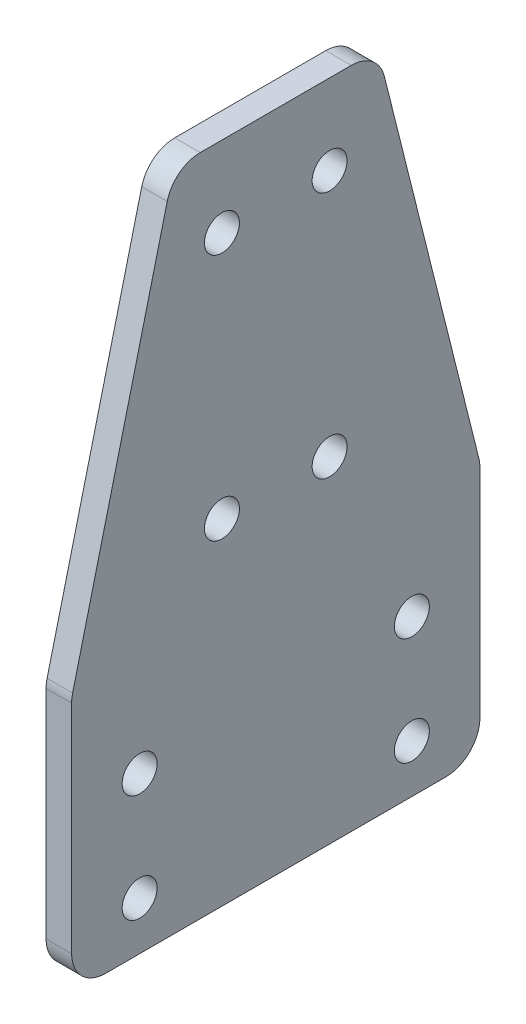
SolidWorks part; units mm, degrees
material "Alloy Steel"
ref_plane "Front Plane" through (0, 0, 0) normal (0, 0, 1) x (1, 0, 0)
ref_plane "Top Plane" through (0, 0, 0) normal (0, 1, 0) x (1, 0, 0)
ref_plane "Right Plane" through (0, 0, 0) normal (1, 0, 0) x (0, 0, -1)
ref_plane "Front Plane-Master Sketch" through (0, 0, 0) normal (0, 0, 1) x (1, 0, 0)
ref_plane "Top Plane-Master Sketch" through (0, 0, 0) normal (0, 1, 0) x (1, 0, 0)
ref_plane "Right Plane-Master Sketch" through (0, 0, 0) normal (1, 0, 0) x (0, 0, -1)
sketch "Y axis top-Master Sketch" plane through (0, 0, 0) normal (0, 1, 0) x (1, 0, 0)
  line L0 (140.4, -200) -> (120.4, -200)
  line L1 (-230.1875, -245) -> (230.1875, -245)
  line L2 (-230.1875, -245) -> (-230.1875, 245)
  line L3 (-230.1875, 245) -> (230.1875, 245)
  line L4 (230.1875, -245) -> (230.1875, 245)
  line L5 (0, 245) -> (0, -245) construction
  line L6 (-230.1875, 0) -> (230.1875, 0) construction
  line L7 (-8, 236.05) -> (8, 236.05)
  line L8 (-8, 236.05) -> (-8, -163.95)
  line L9 (-8, -163.95) -> (8, -163.95)
  line L10 (8, 236.05) -> (8, -163.95)
  line L11 (-140.4, 200) -> (-120.4, 200)
  line L12 (-140.4, 200) -> (-140.4, -200)
  line L13 (-140.4, -200) -> (-120.4, -200)
  line L14 (-120.4, 200) -> (-120.4, -200)
  line L15 (120.4, 200) -> (120.4, -200)
  line L16 (140.4, 200) -> (120.4, 200)
  line L17 (140.4, 200) -> (140.4, -200)
  line L18 (-230.1875, 206.9) -> (230.1875, 206.9)
  line L19 (-230.1875, -206.9) -> (230.1875, -206.9)
  line L20 (-192.0875, 206.9) -> (-192.0875, -206.9)
  line L21 (192.0875, 206.9) -> (192.0875, -206.9)
  line L22 (230.1875, 149.75) -> (192.0875, 149.75)
  line L27 (-152.4, -152.4) -> (152.4, -152.4)
  line L28 (-152.4, -152.4) -> (-152.4, 152.4)
  line L29 (-152.4, 152.4) -> (152.4, 152.4)
  line L34 (152.4, -152.4) -> (152.4, 152.4)
  line L35 (0, 152.4) -> (0, -152.4) construction
  line L36 (-152.4, 0) -> (152.4, 0) construction
  line L37 (-230.1875, 187.85) -> (-192.0875, 187.85)
  line L38 (-230.1875, 187.85) -> (-230.1875, 149.75)
  line L39 (-28.2, 324.7625) -> (28.2, 324.7625)
  line L40 (-28.2, 324.7625) -> (-28.2, 249.7625)
  line L41 (-28.2, 249.7625) -> (28.2, 249.7625)
  line L42 (28.2, 324.7625) -> (28.2, 249.7625)
  line L43 (-26, -20) -> (26, -20)
  line L44 (-26, -20) -> (-26, 20)
  line L45 (-26, 20) -> (26, 20)
  line L46 (26, -20) -> (26, 20)
  line L47 (0, 20) -> (0, -20) construction
  line L48 (-26, 0) -> (26, 0) construction
  line L49 (-230.1875, 149.75) -> (-192.0875, 149.75)
  line L50 (-192.0875, 187.85) -> (-192.0875, 149.75)
  line L51 (192.0875, 187.85) -> (192.0875, 149.75)
  line L52 (230.1875, 187.85) -> (192.0875, 187.85)
  line L53 (230.1875, 187.85) -> (230.1875, 149.75)
  line L55 (-230.1875, 206.9) -> (-234.95, 206.9)
  line L56 (-234.95, 206.9) -> (-234.95, 130.7)
  line L57 (-234.95, 130.7) -> (-230.1875, 130.7)
  point P0 (0, 0)
  point P8 (0, 236.05)
  point P32 (0, 0)
  point P33 (0, 324.7625)
  point P34 (0, 0)
  point P52 (-230.1875, 168.8)
  point P53 (-234.95, 168.8)
  point P56 (-120.4, 0)
  dimension "D3" = 16
  dimension "D4" = 400
  dimension "D5" = 20
  dimension "D6" = 400
  dimension "D7" = 38.1
  dimension "D8" = 38.1
  dimension "D9" = 38.1
  dimension "D10" = 12
  dimension "D11" = 56.4
  dimension "D12" = 75
  dimension "D13" = 4.7625
  dimension "D14" = 304.8
  dimension "D15" = 52
  dimension "D16" = 40
  dimension "D17" = 45
  dimension "D18" = 304.8
  dimension "D19" = 4.7625
  dimension "D20" = 19.05
  dimension "D22" = 8.95
  dimension "D23" = 460.375
ref_plane "X axis plane-Master Sketch" through (-212.3, 0, -100.693) normal (0, 0, -1) x (-1, 0, 0)
sketch "Y axis side-Master Sketch" plane through (0, 0, 0) normal (0, 0, 1) x (1, 0, 0)
  line L0 (-230.1875, 0) -> (-230.1875, 47.625)
  line L3 (-230.1875, 0) -> (-192.0875, 0)
  line L4 (-23.5, 93.125) -> (-23.5, 46.125) construction
  line L6 (-230.1875, 38.1) -> (230.1875, 38.1)
  line L7 (230.1875, 0) -> (230.1875, 47.625)
  line L8 (-192.0875, 0) -> (-192.0875, 38.1)
  line L12 (230.1875, 0) -> (230.1875, 47.625)
  line L14 (230.1875, 0) -> (192.0875, 0)
  line L33 (192.0875, 0) -> (192.0875, 38.1)
  line L34 (-23.5, 46.125) -> (23.5, 46.125) construction
  line L41 (-230.1875, 47.625) -> (230.1875, 47.625)
  line L42 (-140.4, 47.625) -> (-140.4, 65.125)
  line L47 (-140.4, 65.125) -> (-120.4, 65.125)
  line L48 (-120.4, 65.125) -> (-120.4, 47.625)
  line L49 (140.4, 47.625) -> (140.4, 65.125)
  line L50 (140.4, 65.125) -> (120.4, 65.125)
  line L51 (120.4, 65.125) -> (120.4, 47.625)
  line L52 (-28.2, 41.425) -> (-28.2, 97.825)
  line L53 (-28.2, 97.825) -> (28.2, 97.825)
  line L54 (28.2, 97.825) -> (28.2, 41.425)
  line L55 (-152.4, 77.625) -> (-152.4, 52.225)
  line L56 (-152.4, 52.225) -> (-140.4, 52.225)
  line L57 (-152.4, 77.625) -> (-108.4, 77.625)
  line L58 (-108.4, 77.625) -> (-108.4, 52.225)
  line L59 (-108.4, 52.225) -> (-120.4, 52.225)
  line L60 (152.4, 52.225) -> (140.4, 52.225)
  line L61 (152.4, 77.625) -> (152.4, 52.225)
  line L62 (152.4, 77.625) -> (108.4, 77.625)
  line L63 (108.4, 77.625) -> (108.4, 52.225)
  line L64 (108.4, 52.225) -> (120.4, 52.225)
  line L65 (-28.2, 41.425) -> (28.2, 41.425)
  line L66 (-26, 49.625) -> (26, 49.625)
  line L67 (-26, 49.625) -> (-26, 89.625)
  line L68 (-26, 89.625) -> (26, 89.625)
  line L69 (26, 49.625) -> (26, 89.625)
  line L70 (0, 89.625) -> (0, 49.625) construction
  line L71 (-26, 69.625) -> (26, 69.625) construction
  line L73 (-152.4, 77.625) -> (-108.4, 77.625)
  line L74 (-152.4, 77.625) -> (-152.4, 89.625)
  line L75 (-152.4, 89.625) -> (-108.4, 89.625)
  line L76 (-108.4, 77.625) -> (-108.4, 89.625)
  line L77 (108.4, 77.625) -> (152.4, 77.625)
  line L78 (108.4, 77.625) -> (108.4, 89.625)
  line L79 (108.4, 89.625) -> (152.4, 89.625)
  line L80 (152.4, 77.625) -> (152.4, 89.625)
  line L85 (-152.4, 89.625) -> (152.4, 89.625)
  line L86 (-152.4, 89.625) -> (-152.4, 102.325)
  line L87 (-152.4, 102.325) -> (152.4, 102.325)
  line L88 (152.4, 89.625) -> (152.4, 102.325)
  circle A12 centre (0, 69.625) radius 6
  circle A13 centre (-23.5, 93.125) radius 2.5
  circle A14 centre (23.5, 93.125) radius 2.5
  circle A15 centre (23.5, 46.125) radius 2.5
  circle A16 centre (-23.5, 46.125) radius 2.5
  point P16 (0, 46.125)
  point P19 (-23.5, 69.625)
  point P90 (0, 97.825)
  point P91 (-28.2, 69.625)
  point P121 (0, 89.625)
  dimension "D20" = 12
  dimension "D24" = 22
  dimension "D5" = 5
  dimension "D3" = 38.1
  dimension "D4" = 47
  dimension "D16" = 9.525
  dimension "D18" = 17.5
  dimension "D19" = 56.4
  dimension "D21" = 44
  dimension "D22" = 30
  dimension "D23" = 4.6
  dimension "D25" = 40
  dimension "D26" = 52
  dimension "D28" = 12.7
sketch "X axis front-Master Sketch" plane through (-396.45, 0, -100.693) normal (0, 0, -1) x (-1, 0, 0)
  line L0 (-184.15, 47.625) -> (-184.15, 390.525)
  line L1 (-184.15, 390.525) -> (-222.25, 390.525)
  line L2 (-222.25, 390.525) -> (-222.25, 47.625)
  line L4 (-414.3375, 0) -> (-414.3375, 246.425) construction
  line L5 (-644.525, 47.625) -> (-644.525, 390.525)
  line L6 (-644.525, 390.525) -> (-606.425, 390.525)
  line L7 (-606.425, 390.525) -> (-606.425, 47.625)
  line L8 (-222.25, 390.525) -> (-606.425, 390.525)
  line L9 (-222.25, 352.425) -> (-606.425, 352.425)
  line L10 (-222.25, 284.525) -> (-606.425, 284.525)
  line L11 (-222.25, 246.425) -> (-606.425, 246.425)
  line L12 (-414.3375, 390.525) -> (-414.3375, 352.425) construction
  line L13 (-414.3375, 284.525) -> (-414.3375, 246.425) construction
  line L14 (-414.3375, 352.425) -> (-414.3375, 284.525) construction
  line L15 (-614.3375, 381.475) -> (-214.3375, 381.475)
  line L16 (-614.3375, 381.475) -> (-614.3375, 361.475)
  line L17 (-614.3375, 361.475) -> (-214.3375, 361.475)
  line L18 (-214.3375, 381.475) -> (-214.3375, 361.475)
  line L19 (-614.3375, 275.475) -> (-214.3375, 275.475)
  line L20 (-614.3375, 275.475) -> (-614.3375, 255.475)
  line L21 (-614.3375, 255.475) -> (-214.3375, 255.475)
  line L22 (-214.3375, 275.475) -> (-214.3375, 255.475)
  line L23 (-614.3375, 326.475) -> (-214.3375, 326.475)
  line L24 (-614.3375, 326.475) -> (-614.3375, 310.475)
  line L25 (-614.3375, 310.475) -> (-214.3375, 310.475)
  line L26 (-214.3375, 326.475) -> (-214.3375, 310.475)
  line L27 (-184.15, 47.625) -> (-222.25, 47.625)
  line L28 (-606.425, 47.625) -> (-644.525, 47.625)
  line L29 (-434.3375, 344.475) -> (-394.3375, 344.475)
  line L30 (-434.3375, 344.475) -> (-434.3375, 292.475)
  line L31 (-434.3375, 292.475) -> (-394.3375, 292.475)
  line L32 (-394.3375, 344.475) -> (-394.3375, 292.475)
  point P24 (-414.3375, 344.475)
  point P25 (-614.3375, 265.475)
  point P30 (-614.3375, 371.475)
  point P31 (-414.3375, 371.475)
  point P36 (-414.3375, 265.475)
  point P41 (-414.3375, 326.475)
  point P42 (-414.3375, 318.475)
  point P43 (-614.3375, 318.475)
  point P44 (-394.3375, 318.475)
  point P45 (-214.3375, 318.475)
  point P51 (-414.3375, 381.475)
  dimension "D1" = 38.1
  dimension "D2" = 400
  dimension "D3" = 20
  dimension "D4" = 16
  dimension "D5" = 40
  dimension "D6" = 52
  dimension "D7" = 35
  dimension "D8" = 342.9
sketch "X axis side-Master Sketch" plane through (0, 0, 0) normal (1, 0, 0) x (0, 0, -1)
  line L1 (144.9875, 381.475) -> (127.4875, 381.475)
  line L2 (144.9875, 381.475) -> (144.9875, 361.475)
  line L3 (144.9875, 361.475) -> (127.4875, 361.475)
  line L4 (127.4875, 381.475) -> (127.4875, 361.475)
  line L5 (140.3875, 381.475) -> (140.3875, 393.475)
  line L6 (140.3875, 393.475) -> (114.9875, 393.475)
  line L7 (114.9875, 393.475) -> (114.9875, 349.475)
  line L8 (144.9875, 371.475) -> (127.4875, 371.475) construction
  line L10 (140.3875, 349.475) -> (114.9875, 349.475)
  line L11 (140.3875, 361.475) -> (140.3875, 349.475)
  line L12 (149.75, 390.525) -> (144.9875, 390.525)
  line L14 (144.9875, 390.525) -> (144.9875, 352.425)
  line L15 (144.9875, 352.425) -> (149.75, 352.425)
  line L17 (149.75, 318.475) -> (122.9875, 318.475) construction
  line L18 (144.9875, 284.525) -> (149.75, 284.525)
  line L19 (144.9875, 246.425) -> (144.9875, 284.525)
  line L20 (149.75, 246.425) -> (144.9875, 246.425)
  line L21 (140.3875, 275.475) -> (140.3875, 287.475)
  line L22 (140.3875, 287.475) -> (114.9875, 287.475)
  line L23 (114.9875, 243.475) -> (114.9875, 287.475)
  line L24 (140.3875, 243.475) -> (114.9875, 243.475)
  line L25 (140.3875, 255.475) -> (140.3875, 243.475)
  line L26 (127.4875, 255.475) -> (127.4875, 275.475)
  line L27 (144.9875, 275.475) -> (127.4875, 275.475)
  line L28 (144.9875, 255.475) -> (144.9875, 275.475)
  line L29 (144.9875, 255.475) -> (127.4875, 255.475)
  line L31 (102.9875, 344.475) -> (142.9875, 344.475)
  line L32 (102.9875, 344.475) -> (102.9875, 292.475)
  line L33 (102.9875, 292.475) -> (142.9875, 292.475)
  line L34 (142.9875, 344.475) -> (142.9875, 292.475)
  line L35 (102.9875, 493.475) -> (96.6375, 493.475)
  line L36 (102.9875, 493.475) -> (102.9875, 243.475)
  line L37 (102.9875, 243.475) -> (96.6375, 243.475)
  line L38 (96.6375, 493.475) -> (96.6375, 243.475)
  circle A0 centre (122.9875, 318.475) radius 6
  point P14 (114.9875, 265.475)
  point P16 (114.9875, 371.475)
  point P48 (122.9875, 292.475)
  dimension "D7" = 12
  dimension "D9" = 22
  dimension "D1" = 4.7625
  dimension "D2" = 17.5
  dimension "D3" = 12
  dimension "D4" = 12.5
  dimension "D5" = 25.4
  dimension "D6" = 40
  dimension "D8" = 6.35
  dimension "D10" = 250
ref_plane "Z axis front plane-Master Sketch" through (0, 556.975, -47.5805) normal (0, 0, 1) x (1, 0, 0)
sketch "Z axis front-Master Sketch" plane through (0, 556.975, -47.5805) normal (0, 0, 1) x (1, 0, 0)
  line L0 (0, 48.55) -> (0, -276.85) construction
  line L1 (-103, 48.55) -> (103, 48.55)
  line L2 (-103, 48.55) -> (-103, -276.85)
  line L3 (-103, -276.85) -> (103, -276.85)
  line L4 (103, 48.55) -> (103, -276.85)
  line L5 (-88, 35.85) -> (-68, 35.85)
  line L6 (-88, 35.85) -> (-88, -264.15)
  line L7 (-88, -264.15) -> (-68, -264.15)
  line L8 (-68, 35.85) -> (-68, -264.15)
  line L9 (88, -264.15) -> (68, -264.15)
  line L10 (68, 35.85) -> (68, -264.15)
  line L11 (88, 35.85) -> (68, 35.85)
  line L12 (88, 35.85) -> (88, -264.15)
  line L13 (-103, -114.15) -> (103, -114.15) construction
  line L14 (-8, -20.3536) -> (8, -20.3536)
  line L15 (-8, -20.3536) -> (-8, -229.2947)
  line L16 (-8, -229.2947) -> (8, -229.2947)
  line L17 (8, -20.3536) -> (8, -229.2947)
  line L19 (-26, -43.6221) -> (26, -43.6221)
  line L20 (-26, -43.6221) -> (-26, -83.6221)
  line L21 (-26, -83.6221) -> (26, -83.6221)
  line L22 (26, -43.6221) -> (26, -83.6221)
  point P20 (0, -20.3536)
  point P27 (0, -43.6221)
  dimension "D1" = 15
  dimension "D2" = 20
  dimension "D3" = 300
  dimension "D4" = 16
  dimension "D5" = 40
  dimension "D6" = 52
  dimension "D7" = 42
  dimension "D8" = 12.7
  dimension "D10" = 12.7
ref_plane "Z axis side plane-Master Sketch" through (-101, 417.8187, -47.5805) normal (0, -1, 0) x (-1, 0, 0)
inserted part "Master Sketch"
move or copy body "Body-Move/Copy2"
ref_plane "Plane1" through (-230.1875, 0, 0) normal (1, 0, 0) x (0, 0, -1)
sketch "Sketch1" plane through (-230.1875, 0, 0) normal (1, 0, 0) x (0, 0, -1)
  line L0 (130.7, 0) -> (206.9, 0)
  line L1 (-245, 0) -> (245, 0) construction
  line L2 (-245, 0) -> (245, 0) construction
  line L3 (187.85, 0) -> (149.75, 0) construction
  line L4 (206.9, 0) -> (206.9, 47.625)
  line L6 (130.7, 47.625) -> (130.7, 0)
  line L7 (206.9, 47.625) -> (187.85, 123.825)
  line L8 (187.85, 123.825) -> (149.75, 123.825)
  line L9 (149.75, 123.825) -> (130.7, 47.625)
  line L11 (143.4, 38.1) -> (-238.65, 38.1) construction
  line L13 (158.75, 108.825) -> (158.75, 123.825) construction
  line L15 (149.75, 390.525) -> (149.75, 38.1) construction
  line L16 (168.8, 123.825) -> (168.8, 0) construction
  line L17 (178.85, 108.825) -> (158.75, 108.825) construction
  line L18 (238.65, 47.625) -> (194.2, 47.625) construction
  circle A0 centre (194.2, 29.1) radius 3.2639
  circle A2 centre (158.75, 108.825) radius 3.2639
  circle A5 centre (178.85, 108.825) radius 3.2639
  circle A6 centre (178.85, 85.725) radius 3.2639 construction
  circle A7 centre (178.85, 62.625) radius 3.2639
  circle A8 centre (158.75, 85.725) radius 3.2639 construction
  circle A9 centre (158.75, 62.625) radius 3.2639
  circle A10 centre (168.8, 29.1) radius 3.2639 construction
  circle A11 centre (143.4, 29.1) radius 3.2639
  circle A12 centre (168.8, 9) radius 3.2639 construction
  circle A13 centre (143.4, 9) radius 3.2639
  circle A14 centre (194.2, 9) radius 3.2639
  point P8 (168.8, 0)
  point P9 (168.8, 123.825)
  point P44 (168.8, 108.825)
  dimension "D3" = 6.5278
  dimension "D2" = 76.2
  dimension "D7" = 12.7
  dimension "D1" = 15
  dimension "D4" = 9
  dimension "D8" = 15
  dimension "D9" = 9
  dimension "D10" = 9
  dimension "D12" = 2
  dimension "D5" = 3
  dimension "D11" = 3
  dimension "D6" = 2
extrude "Boss-Extrude1" add sketch "Sketch1" against normal up to vertex
sketch "Sketch3" plane through (-234.95, 0, 0) normal (-1, 0, 0) x (0, 0, 1)
  line L0 (-187.85, 123.825) -> (-187.85, 198.825)
  line L1 (-187.85, 198.825) -> (-149.75, 198.825)
  line L2 (-149.75, 198.825) -> (-30.7, 38.1)
  line L3 (-30.7, 38.1) -> (-30.7, 0)
  line L4 (-30.7, 0) -> (-130.7, 0)
  line L5 (-130.7, 47.625) -> (-130.7, 0) construction
  line L6 (-149.75, 123.825) -> (-130.7, 47.625) construction
  line L7 (-187.85, 123.825) -> (-149.75, 123.825) construction
  line L8 (-130.7, 47.625) -> (-130.7, 0)
  line L9 (-149.75, 123.825) -> (-130.7, 47.625)
  line L10 (-187.85, 123.825) -> (-149.75, 123.825)
  line L11 (-178.85, 108.825) -> (-178.85, 62.625) construction
  line L12 (-158.75, 108.825) -> (-158.75, 62.625) construction
  line L13 (-178.85, 198.825) -> (-178.85, 189.825) construction
  line L14 (-178.85, 189.825) -> (-187.85, 189.825) construction
  line L15 (-178.85, 108.825) -> (-178.85, 149.325) construction
  line L16 (-178.85, 149.325) -> (-178.85, 189.825) construction
  line L17 (-194.2, 9) -> (-143.4, 9) construction
  line L18 (-143.4, 29.1) -> (-194.2, 29.1) construction
  line L19 (-143.4, 29.1) -> (-91.55, 29.1) construction
  line L20 (-91.55, 29.1) -> (-39.7, 29.1) construction
  line L21 (-39.7, 9) -> (-30.7, 9) construction
  line L22 (-39.7, 9) -> (-39.7, 0) construction
  circle A0 centre (-158.75, 108.825) radius 3.2639 construction
  circle A1 centre (-178.85, 62.625) radius 3.2639 construction
  circle A2 centre (-178.85, 149.325) radius 3.2639
  circle A3 centre (-178.85, 189.825) radius 3.2639
  circle A4 centre (-158.75, 189.825) radius 3.2639
  circle A5 centre (-158.75, 149.325) radius 3.2639
  circle A6 centre (-91.55, 29.1) radius 3.2639
  circle A7 centre (-39.7, 29.1) radius 3.2639
  circle A8 centre (-39.7, 9) radius 3.2639
  circle A9 centre (-91.55, 9) radius 3.2639
  circle A10 centre (-143.4, 29.1) radius 3.2639 construction
  dimension "D1" = 100
  dimension "D2" = 75
extrude "Boss-Extrude2" [suppressed] add sketch "Sketch3" against normal up to surface (4.7625 mm away)
fillet "Fillet1" radius 6.35 6 edges at (-232.5687, 0, -130.7) (-232.5687, 0, -206.9) (-232.5687, 47.625, -206.9) (-232.5687, 47.625, -130.7) (-232.5687, 123.825, -187.85) (-232.5687, 123.825, -149.75)
fillet "Fillet2" [suppressed] radius 10
equation "\"D3@Sketch1\"=.257in"
